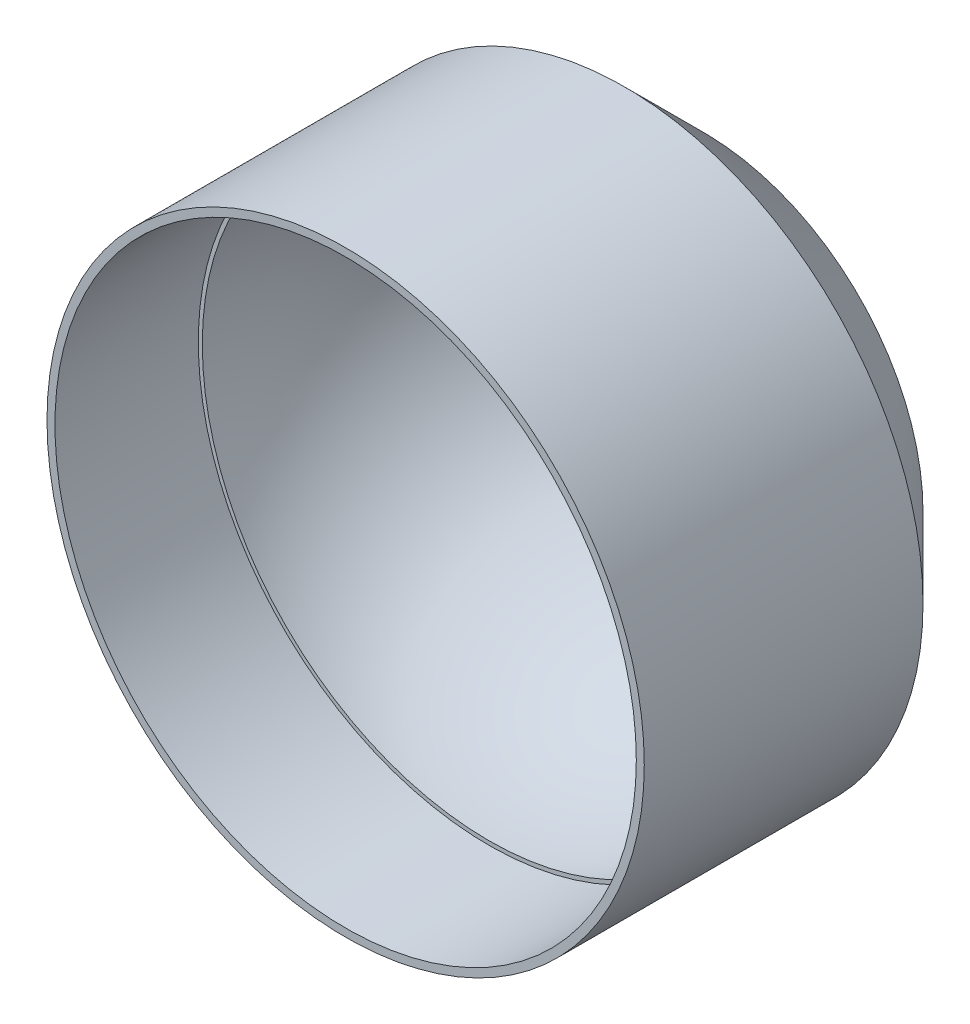
SolidWorks part; units mm, degrees
ref_plane "Front Plane" through (0, 0, 0) normal (0, 0, 1) x (1, 0, 0)
ref_plane "Top Plane" through (0, 0, 0) normal (0, 1, 0) x (1, 0, 0)
ref_plane "Right Plane" through (0, 0, 0) normal (1, 0, 0) x (0, 0, -1)
sketch "Sketch1" plane through (0, 0, 0) normal (0, 0, 1) x (1, 0, 0)
  circle A0 centre (0, 0) radius 37.5
  dimension "D1" = 75
extrude "Boss-Extrude1" add sketch "Sketch1" along normal blind 45
sketch "Sketch5" plane through (0, 0, 45) normal (0, 0, 1) x (1, 0, 0)
  circle A0 centre (0, 0) radius 36.5
  dimension "D1" = 73
extrude "Cut-Extrude2" cut sketch "Sketch5" against normal blind 18
ref_plane "Plane1" through (0, 0, 27) normal (0, 0, 1) x (1, 0, 0)
sketch "Sketch7" plane through (0, 0, 27) normal (0, 0, 1) x (1, 0, 0)
  line L0 (-36, 0) -> (36, 0)
  line L1 (0, 8.9792) -> (0, -9.4282) construction
  arc A0 (-36, 0) -> (36, 0) centre (0, 0) cw
  point P6 (0, 0)
  dimension "D1" = 72
revolve "Cut-Revolve3" cut sketch "Sketch7" angle 180 about L0
chamfer "Chamfer1" distance 10 angle 45 1 edges at (37.5, 0, 0)
